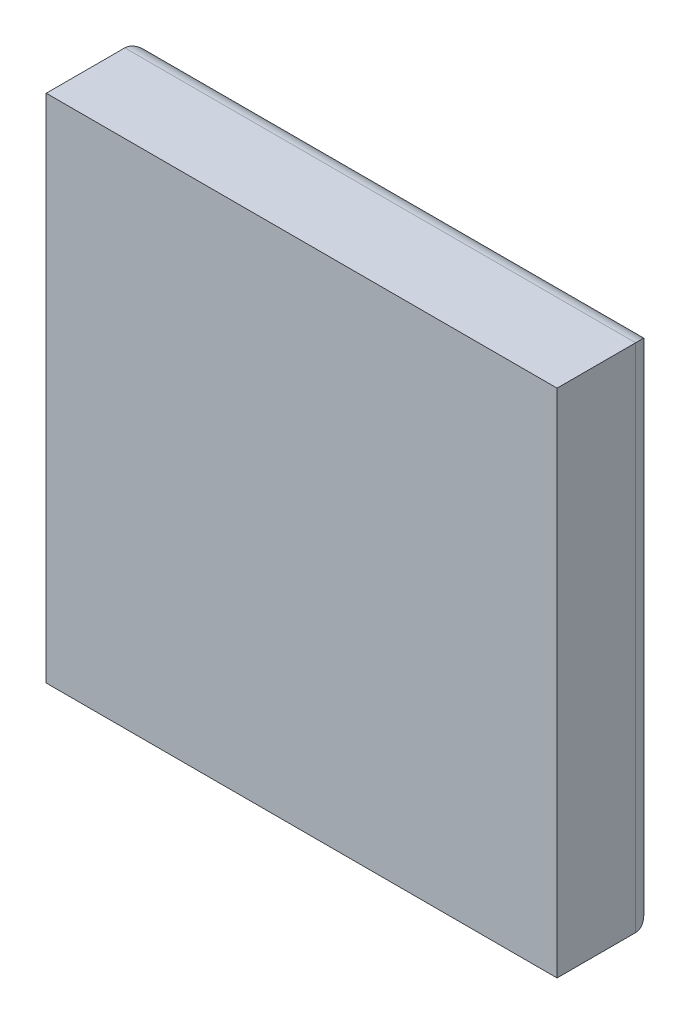
SolidWorks part; units mm, degrees
ref_plane "Plano frontal" through (0, 0, 0) normal (0, 0, 1) x (1, 0, 0)
ref_plane "Plano superior" through (0, 0, 0) normal (0, 1, 0) x (1, 0, 0)
ref_plane "Plano direito" through (0, 0, 0) normal (1, 0, 0) x (0, 0, -1)
sketch "Esboço1" plane through (0, 0, 0) normal (0, 0, 1) x (1, 0, 0)
  line L1 (-36.8398, -1.1369) -> (-10.8398, -1.1369)
  line L2 (-36.8398, -1.1369) -> (-36.8398, -27.1369)
  line L3 (-36.8398, -27.1369) -> (-10.8398, -27.1369)
  line L4 (-10.8398, -1.1369) -> (-10.8398, -27.1369)
  dimension "D1" = 26
  dimension "D2" = 26
extrude "Ressalto-extrusão1" add sketch "Esboço1" along normal blind 5
fillet "Filete1" radius 1 4 edges at (-23.8398, -27.1369, 0) (-23.8398, -1.1369, 0) (-10.8398, -14.1369, 0) (-36.8398, -14.1369, 0)
